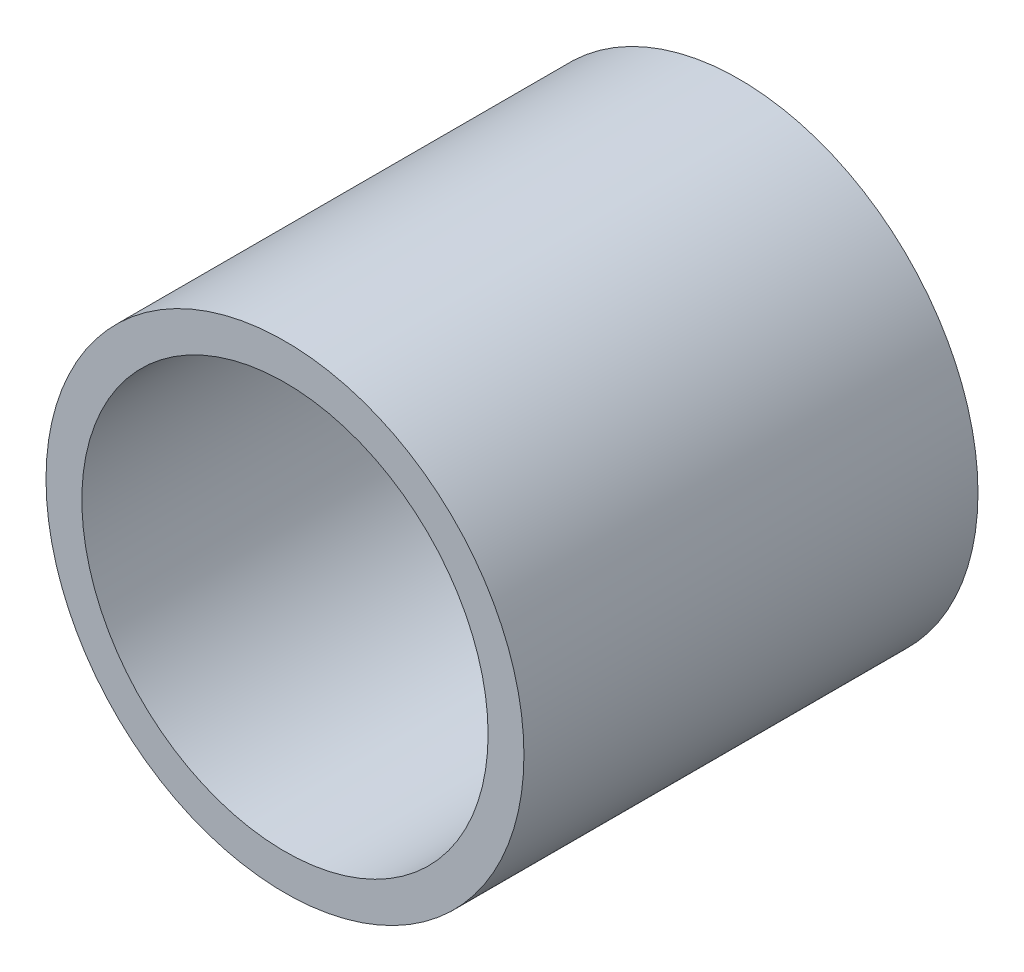
SolidWorks part; units mm, degrees
material "1023 Carbon Steel Sheet (SS)"
ref_plane "Front" through (0, 0, 0) normal (0, 0, 1) x (1, 0, 0)
ref_plane "Top" through (0, 0, 0) normal (0, 1, 0) x (1, 0, 0)
ref_plane "Right" through (0, 0, 0) normal (1, 0, 0) x (0, 0, -1)
sketch "Sketch1" plane through (0, 0, 0) normal (0, 0, 1) x (1, 0, 0)
  circle A0 centre (0, 0) radius 20
  circle A1 centre (0, 0) radius 17
  dimension "D1" = 40
  dimension "D2" = 34
extrude "Boss-Extrude1" add sketch "Sketch1" along normal blind 38
